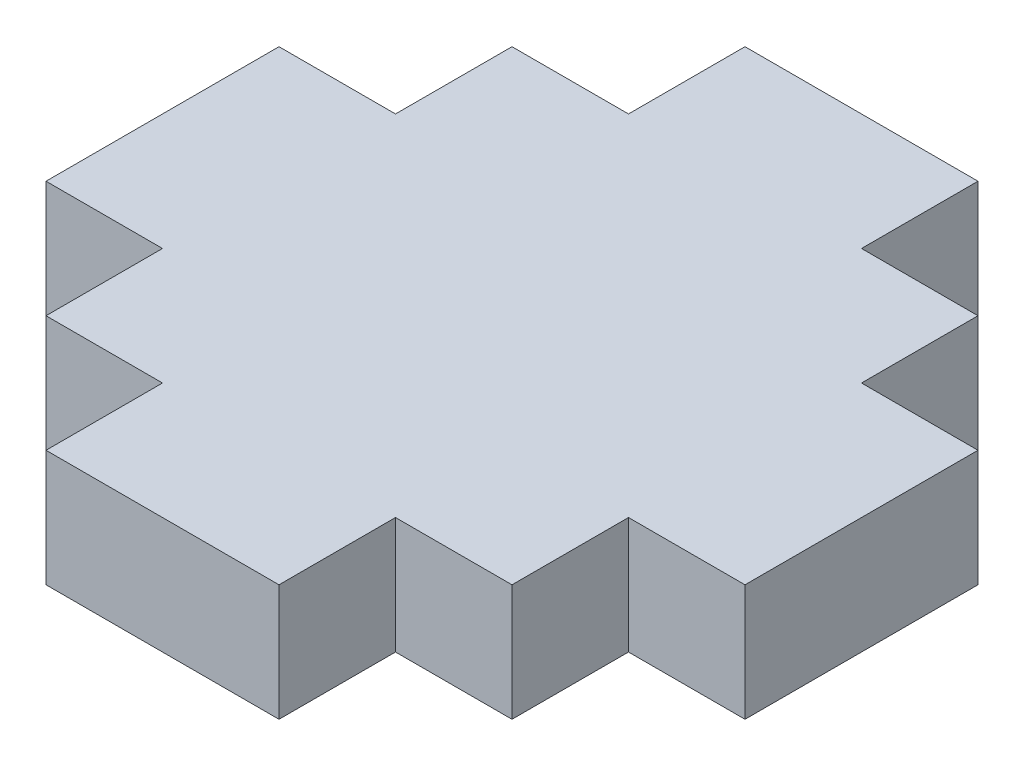
SolidWorks part; units mm, degrees
material "Acrylic (Medium-high impact)"
ref_plane "Plano frontal" through (0, 0, 0) normal (0, 0, 1) x (1, 0, 0)
ref_plane "Plano superior" through (0, 0, 0) normal (0, 1, 0) x (1, 0, 0)
ref_plane "Plano direito" through (0, 0, 0) normal (1, 0, 0) x (0, 0, -1)
sketch "Sketch1" plane through (0, 0, 0) normal (0, 1, 0) x (1, 0, 0)
  line L1 (-6, 6) -> (6, 6)
  line L2 (-6, 6) -> (-6, -6)
  line L3 (-6, -6) -> (6, -6)
  line L4 (6, 6) -> (6, -6)
  point P4 (0, 6)
  point P6 (-6, 0)
  dimension "D1" = 12
  dimension "D2" = 12
extrude "Boss-Extrude1" add sketch "Sketch1" along normal mid plane 3
sketch "Sketch2" plane through (0, 0, 0) normal (0, 1, 0) x (1, 0, 0)
  line L0 (6, 6) -> (-6, 6) construction
  line L1 (-3, 6) -> (3, 6)
  line L2 (-3, 6) -> (-3, 9)
  line L3 (-3, 9) -> (3, 9)
  line L4 (3, 6) -> (3, 9)
  line L5 (-1.65, 0) -> (1.65, 0) construction
  line L6 (3, -6) -> (3, -9)
  line L7 (-3, -9) -> (3, -9)
  line L8 (-3, -6) -> (-3, -9)
  line L9 (-3, -6) -> (3, -6)
  line L10 (-6, 6) -> (-6, -6) construction
  line L11 (-6, 3) -> (-9, 3)
  line L12 (-6, 3) -> (-6, -3)
  line L13 (-6, -3) -> (-9, -3)
  line L14 (-9, 3) -> (-9, -3)
  line L15 (0, -1.65) -> (0, 1.65) construction
  line L16 (9, 3) -> (9, -3)
  line L17 (6, -3) -> (9, -3)
  line L18 (6, 3) -> (6, -3)
  line L19 (6, 3) -> (9, 3)
  point P6 (0, 6)
  point P20 (-9, 0)
  dimension "D1" = 3
  dimension "D2" = 6
  dimension "D3" = 6
extrude "Boss-Extrude2" add sketch "Sketch2" along normal mid plane 3
